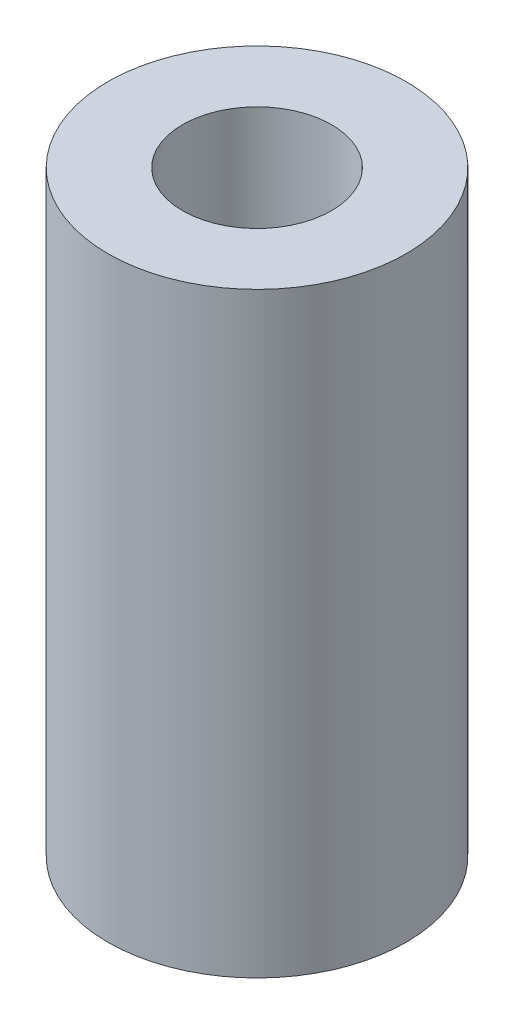
SolidWorks part; units mm, degrees
material "Polycarbonate"
ref_plane "Front Plane" through (0, 0, 0) normal (0, 0, 1) x (1, 0, 0)
ref_plane "Top Plane" through (0, 0, 0) normal (0, 1, 0) x (1, 0, 0)
ref_plane "Right Plane" through (0, 0, 0) normal (1, 0, 0) x (0, 0, -1)
sketch "Sketch1" plane through (0, 0, 0) normal (0, 1, 0) x (1, 0, 0)
  circle A0 centre (0, 0) radius 0.7937
  circle A1 centre (0, 0) radius 1.5875
  dimension "D1" = 1.5875
  dimension "D2" = 3.175
extrude "Boss-Extrude1" add sketch "Sketch1" along normal blind 6.35
